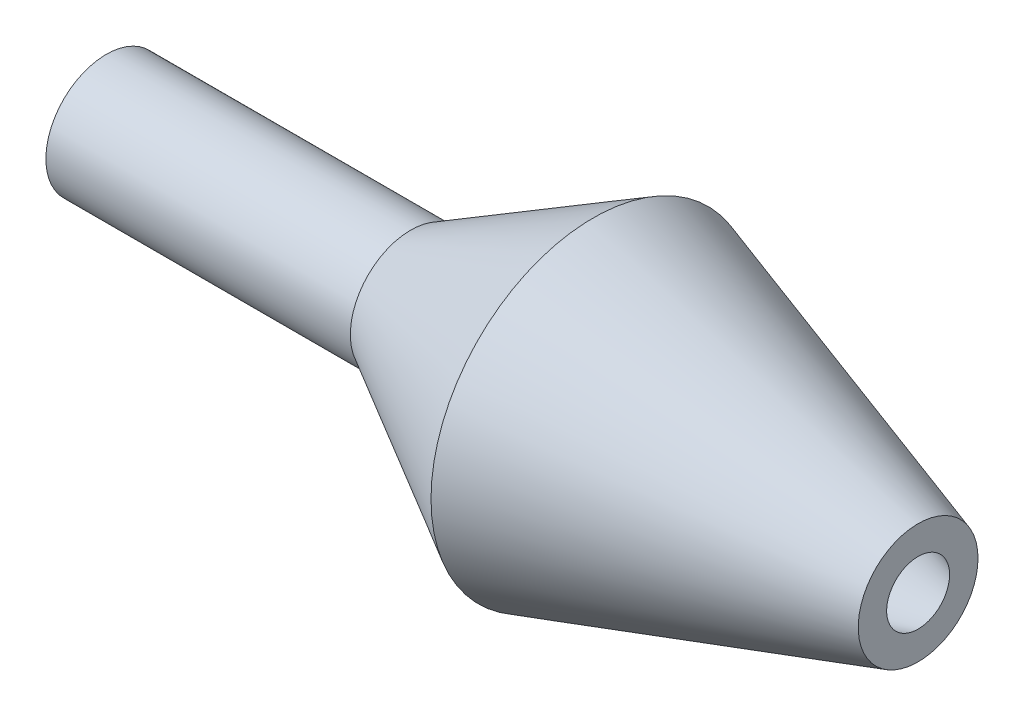
SolidWorks part; units mm, degrees
ref_plane "Front Plane" through (0, 0, 0) normal (0, 0, 1) x (1, 0, 0)
ref_plane "Top Plane" through (0, 0, 0) normal (0, 1, 0) x (1, 0, 0)
ref_plane "Right Plane" through (0, 0, 0) normal (1, 0, 0) x (0, 0, -1)
sketch "Sketch1" plane through (0, 0, 0) normal (0, 1, 0) x (1, 0, 0)
  line L0 (0, 0) -> (-40, 0) construction
  line L1 (-40, 1.575) -> (-25, 1.575)
  line L3 (-16, 8) -> (0, 2.95)
  line L4 (-40, 2.975) -> (-25, 2.975)
  line L5 (-25, 2.975) -> (-16, 8)
  line L6 (0, 1.55) -> (-16, 6.6)
  line L7 (-16, 6.6) -> (-25, 1.575)
  line L9 (-40, 2.975) -> (-40, 1.575)
  line L10 (0, 2.95) -> (0, 1.55)
  point P11 (0, 0)
  point P12 (0, 0)
  point P13 (0, 0)
  point P14 (0, 0)
  point P15 (-38.8723, 1.4)
  point P16 (0, 0)
  dimension "D1" = 40
  dimension "D3" = 1.575
  dimension "D4" = 2.95
  dimension "D5" = 8
  dimension "D6" = 1.4
  dimension "D7" = 1.4
  dimension "D8" = 1.4
  dimension "D9" = 15
  dimension "D10" = 16
revolve "Revolve1" add sketch "Sketch1" angle 360 about L0
